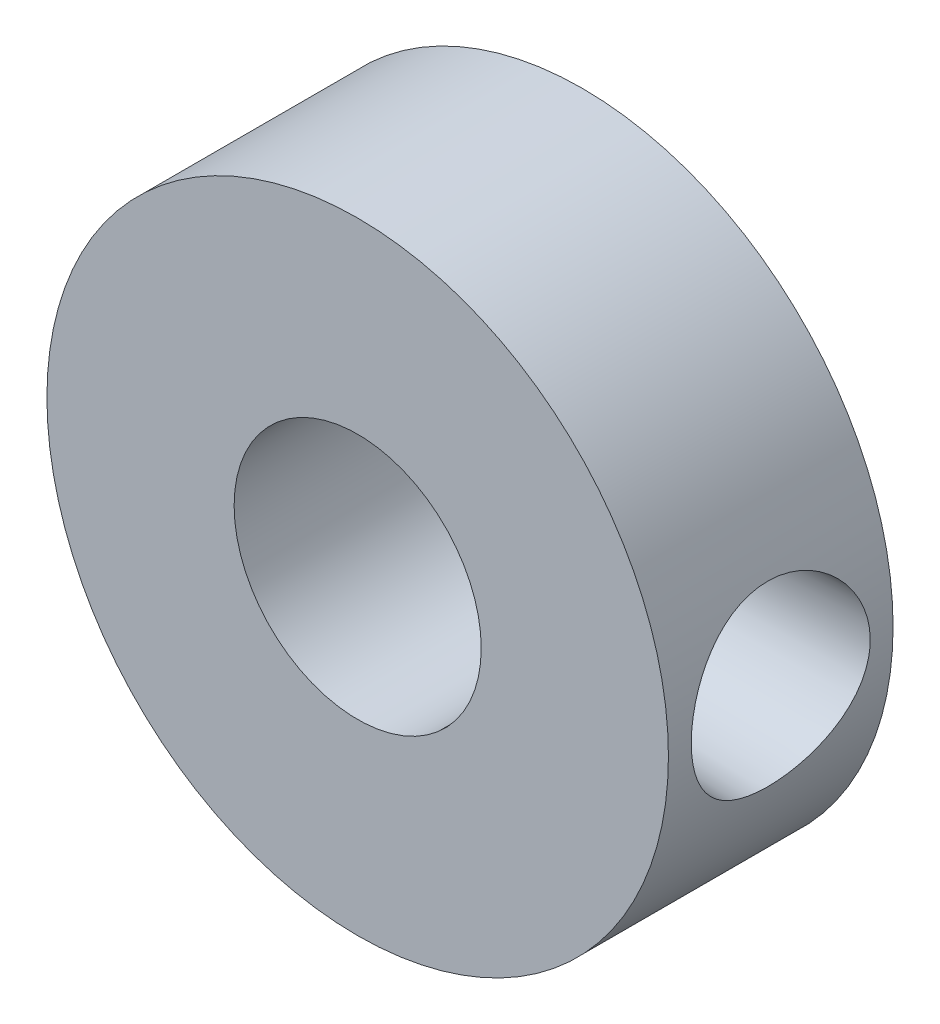
SolidWorks part; units mm, degrees
ref_plane "Front Plane" through (0, 0, 0) normal (0, 0, 1) x (1, 0, 0)
ref_plane "Top Plane" through (0, 0, 0) normal (0, 1, 0) x (1, 0, 0)
ref_plane "Right Plane" through (0, 0, 0) normal (1, 0, 0) x (0, 0, -1)
sketch "Sketch1" plane through (0, 0, 0) normal (0, 0, 1) x (1, 0, 0)
  circle A0 centre (0, 0) radius 4.191
  circle A1 centre (0, 0) radius 10.541
  dimension "D1" = 8.382
  dimension "D2" = 6.35
extrude "Boss-Extrude1" add sketch "Sketch1" along normal blind 7.62
sketch "Sketch2" plane through (0, 0, 0) normal (1, 0, 0) x (0, 0, -1)
  line L0 (-3.81, -10.541) -> (-3.81, 0) construction
  line L1 (-7.62, -10.541) -> (0, -10.541) construction
  circle A0 centre (-3.81, 0) radius 2.667
  dimension "D1" = 5.334
extrude "Cut-Extrude1" cut sketch "Sketch2" along normal through all draft 2 draft outward yes
